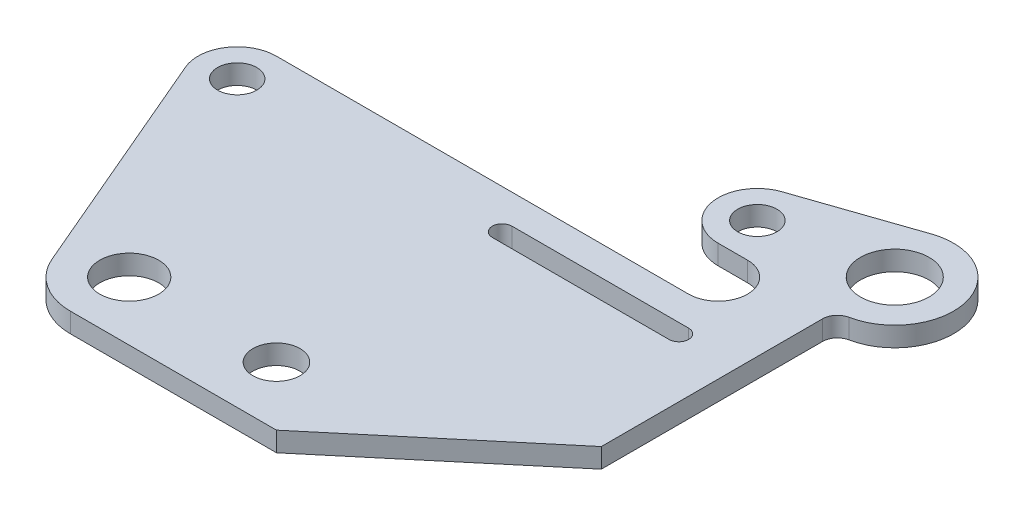
SolidWorks part; units mm, degrees
material "AISI 1020"
ref_plane "Front Plane" through (0, 0, 0) normal (0, 0, 1) x (1, 0, 0)
ref_plane "Top Plane" through (0, 0, 0) normal (0, 1, 0) x (1, 0, 0)
ref_plane "Right Plane" through (0, 0, 0) normal (1, 0, 0) x (0, 0, -1)
sketch "Sketch1" plane through (0, 0, 0) normal (0, 1, 0) x (1, 0, 0)
  line L0 (-199.1161, 272.1438) -> (-70.0741, -29.9343)
  line L1 (0, -76.2) -> (266.7, -76.2)
  line L2 (266.7, -76.2) -> (495.3, 115.6182)
  line L3 (495.3, 115.6182) -> (495.3, 401.9744)
  line L4 (-152.4, 342.9) -> (381, 342.9)
  line L5 (342.9, 419.1) -> (381, 419.1)
  line L6 (326.4243, 517.9541) -> (470.5865, 567.3811)
  line L7 (0, 0) -> (190.5, 0) construction
  line L8 (190.5, 292.1) -> (419.1, 292.1) construction
  line L9 (190.5, 304.8) -> (419.1, 304.8)
  line L10 (190.5, 279.4) -> (419.1, 279.4)
  arc A1 (-70.0741, -29.9343) -> (0, -76.2) centre (0, 0) ccw
  arc A2 (-152.4, 342.9) -> (-199.1161, 272.1438) centre (-152.4, 292.1) ccw
  arc A4 (381, 342.9) -> (381, 419.1) centre (381, 381) ccw
  arc A5 (326.4243, 517.9541) -> (342.9, 419.1) centre (342.9, 469.9) ccw
  arc A6 (510.54, 420.6396) -> (470.5865, 567.3811) centre (495.3, 495.3) ccw
  arc A7 (495.3, 401.9744) -> (510.54, 420.6396) centre (514.35, 401.9744) cw
  circle A8 centre (-152.4, 292.1) radius 25.4
  circle A9 centre (0, 0) radius 38.1
  circle A10 centre (342.9, 469.9) radius 25.4
  circle A11 centre (495.3, 495.3) radius 44.45
  circle A12 centre (190.5, 0) radius 30.48
  arc A13 (190.5, 304.8) -> (190.5, 279.4) centre (190.5, 292.1) ccw
  arc A14 (419.1, 279.4) -> (419.1, 304.8) centre (419.1, 292.1) ccw
  point P28 (304.8, 292.1)
  dimension "D1" = 152.4
  dimension "D2" = 140
  dimension "D3" = 101.6
  dimension "D4" = 266.7
  dimension "D7" = 228.6
  dimension "D8" = 152.4
  dimension "D11" = 101.6
  dimension "D12" = 76.2
  dimension "D13" = 152.4
  dimension "D14" = 19.05
  dimension "D15" = 114.3
  dimension "D17" = 50.8
  dimension "D18" = 76.2
  dimension "D19" = 50.8
  dimension "D20" = 88.9
  dimension "D22" = 60.96
  dimension "D5" = 292.1
  dimension "D6" = 152.4
  dimension "D9" = 38.1
  dimension "D10" = 177.8
  dimension "D16" = 107.7631
  dimension "D21" = 190.5
  dimension "D23" = 228.6
  dimension "D24" = 25.4
extrude "Boss-Extrude1" add sketch "Sketch1" along normal mid plane 25.4
